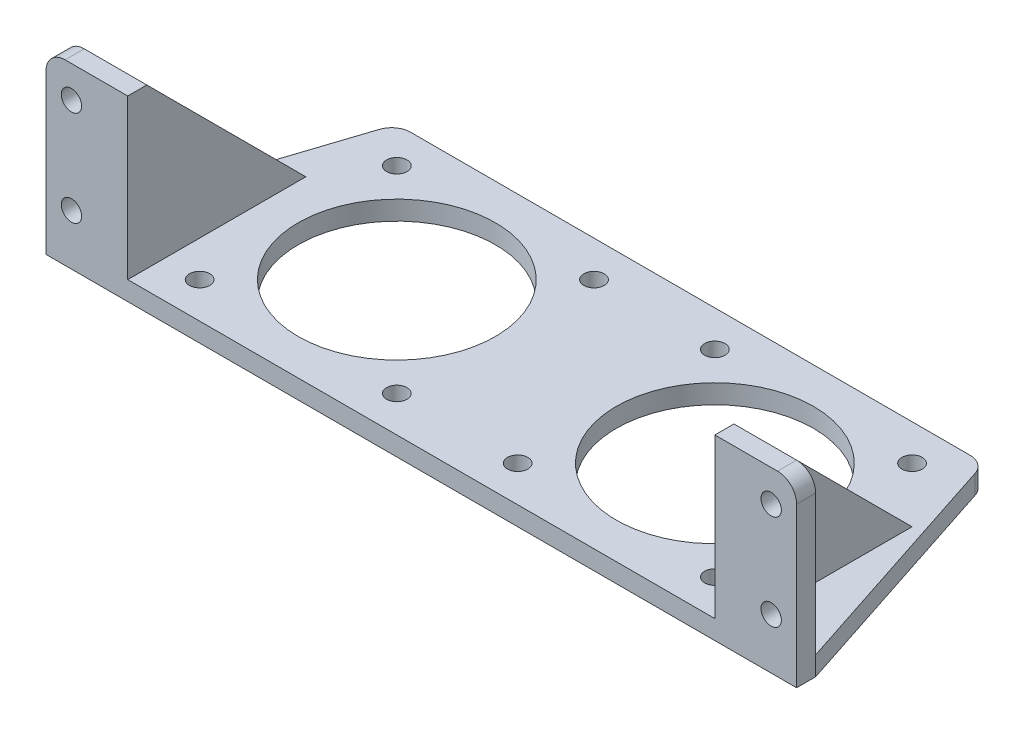
SolidWorks part; units mm, degrees
ref_plane "Front Plane" through (0, 0, 0) normal (0, 0, 1) x (1, 0, 0)
ref_plane "Top Plane" through (0, 0, 0) normal (0, 1, 0) x (1, 0, 0)
ref_plane "Right Plane" through (0, 0, 0) normal (1, 0, 0) x (0, 0, -1)
sketch "Sketch1" plane through (0, 0, 0) normal (0, 1, 0) x (1, 0, 0)
  line L0 (46.15, 13.8493) -> (-46.15, 13.8493)
  line L1 (-46.15, 13.8493) -> (-59, -25.4507)
  line L2 (-59, -25.4507) -> (-59, -28.4507)
  line L3 (-59, -28.4507) -> (59, -28.4507)
  line L4 (59, -28.4507) -> (59, -25.4507)
  line L5 (59, -25.4507) -> (46.15, 13.8493)
  line L7 (-46.15, 13.8493) -> (-3.85, 13.8493) construction
  line L8 (-46.15, 13.8493) -> (-46.15, -28.4507) construction
  line L9 (-46.15, -28.4507) -> (-3.85, -28.4507) construction
  line L10 (-3.85, 13.8493) -> (-3.85, -28.4507) construction
  line L11 (-3.85, 13.8493) -> (-46.15, -28.4507) construction
  line L12 (-46.15, 13.8493) -> (-3.85, -28.4507) construction
  line L13 (0, 13.8493) -> (0, -28.4507) construction
  line L14 (-40.5, -22.8007) -> (-9.5, -22.8007) construction
  line L15 (-40.5, -22.8007) -> (-40.5, 8.1993) construction
  line L16 (-40.5, 8.1993) -> (-9.5, 8.1993) construction
  line L17 (-9.5, -22.8007) -> (-9.5, 8.1993) construction
  line L18 (-40.5, -22.8007) -> (-9.5, 8.1993) construction
  line L19 (-40.5, 8.1993) -> (-9.5, -22.8007) construction
  circle A0 centre (-40.5, 8.1993) radius 1.6
  circle A1 centre (-9.5, 8.1993) radius 1.6
  circle A2 centre (-40.5, -22.8007) radius 1.6
  circle A3 centre (-9.5, -22.8007) radius 1.6
  circle A4 centre (-25, -7.3007) radius 15.5
  circle A5 centre (40.5, -22.8007) radius 1.6
  circle A6 centre (9.5, -22.8007) radius 1.6
  circle A7 centre (9.5, 8.1993) radius 1.6
  circle A8 centre (40.5, 8.1993) radius 1.6
  circle A9 centre (25, -7.3007) radius 15.5
  point P2 (0, -28.4507)
  point P7 (0, 13.8493)
  point P13 (-25, -7.3007)
  dimension "D1" = 42.3
  dimension "D7" = 3.2
  dimension "D2" = 3
  dimension "D3" = 92.3
  dimension "D4" = 118
  dimension "D5" = 42.3
  dimension "D6" = 31
extrude "Boss-Extrude1" add sketch "Sketch1" along normal blind 3
sketch "Sketch2" plane through (0, 3, 0) normal (0, 1, 0) x (1, 0, 0)
  line L1 (-59, -28.4507) -> (-46.15, -28.4507)
  line L2 (-59, -28.4507) -> (-59, -25.4507)
  line L3 (-59, -25.4507) -> (-46.15, -25.4507)
  line L4 (-46.15, -28.4507) -> (-46.15, -25.4507)
extrude "Boss-Extrude2" add sketch "Sketch2" along normal blind 25
sketch "Sketch3" plane through (0, 0, 25.4507) normal (0, 0, -1) x (-1, 0, 0)
  line L0 (59, 15.5) -> (46.15, 15.5) construction
  line L1 (59, 28) -> (59, 3) construction
  line L2 (46.15, 28) -> (46.15, 3) construction
  circle A0 centre (55, 8) radius 1.6
  circle A1 centre (55, 23) radius 1.6
  dimension "D2" = 3.2
  dimension "D3" = 15
  dimension "D1" = 55
extrude "Cut-Extrude1" cut sketch "Sketch3" against normal through all
sketch "Sketch4" plane through (-46.15, 0, 0) normal (1, 0, 0) x (0, 0, -1)
  line L0 (-25.4507, 28) -> (-0.4507, 3)
  line L1 (-25.4507, 3) -> (13.8493, 3) construction
  line L2 (-0.4507, 3) -> (-25.4507, 3)
  line L3 (-25.4507, 3) -> (-25.4507, 28)
extrude "Boss-Extrude3" add sketch "Sketch4" against normal blind 3
chamfer "Chamfer1" distance 2 angle 45 1 edges at (-49.15, 15.5, 25.4507)
fillet "Fillet1" radius 3 1 edges at (-59, 28, 26.9507)
fillet "Fillet2" radius 3 2 edges at (46.15, 1.5, -13.8493) (-46.15, 1.5, -13.8493)
mirror "Mirror1" about plane through (0, 0, 0) normal (1, 0, 0) of "Fillet1", "Chamfer1", "Boss-Extrude3", "Cut-Extrude1", "Boss-Extrude2"
